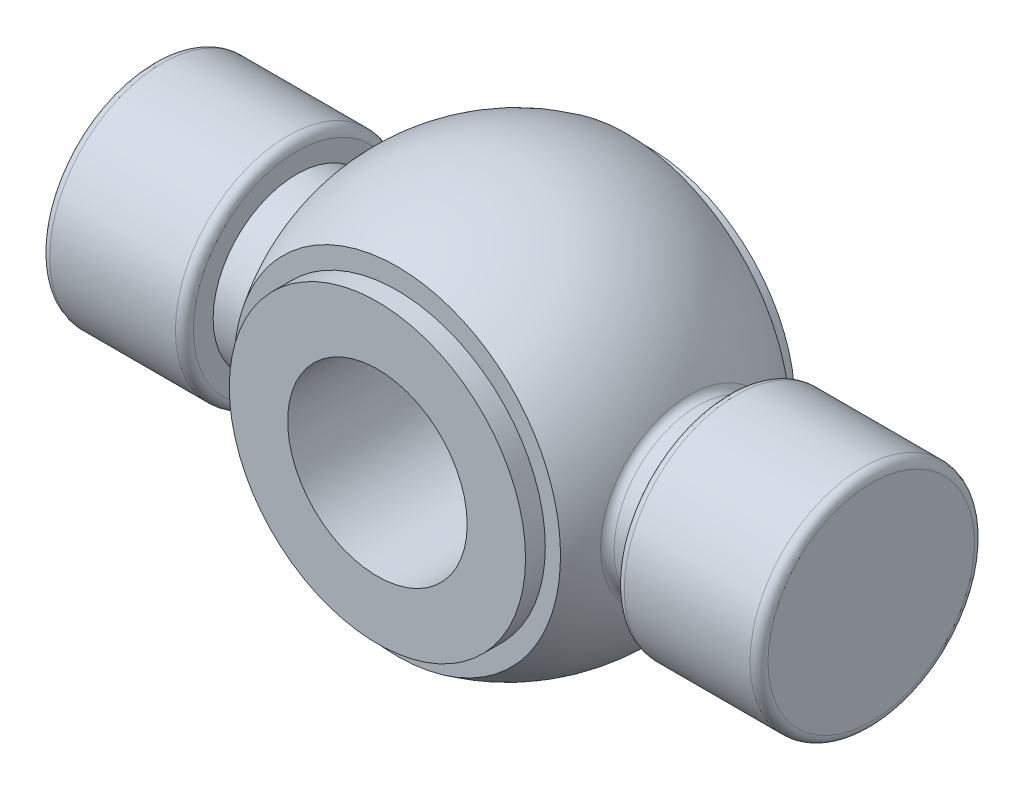
SolidWorks part; units mm, degrees
ref_plane "Front" through (0, 0, 0) normal (0, 0, 1) x (1, 0, 0)
ref_plane "Top" through (0, 0, 0) normal (0, 1, 0) x (1, 0, 0)
ref_plane "Right" through (0, 0, 0) normal (1, 0, 0) x (0, 0, -1)
sketch "Sketch1" plane through (0, 0, 0) normal (0, 0, 1) x (1, 0, 0)
  line L0 (-25.4, 0) -> (-25.4, 7.9375)
  line L1 (-25.4, 7.9375) -> (-15.24, 7.9375)
  line L2 (-12.7, 5.9055) -> (12.7, 5.9055) construction
  line L3 (12.7, 5.9055) -> (15.24, 5.9055)
  line L4 (25.4, 7.9375) -> (25.4, 0)
  line L5 (25.4, 0) -> (-25.4, 0)
  line L6 (-40.557, 0) -> (103.3272, 0) construction
  line L7 (0, 0) -> (0, 48.3914) construction
  line L8 (-15.24, 7.9375) -> (-15.24, 5.9055)
  line L9 (-15.24, 5.9055) -> (-12.7, 5.9055)
  line L10 (15.24, 5.9055) -> (15.24, 7.9375)
  line L11 (15.24, 7.9375) -> (25.4, 7.9375)
  arc A0 (12.7, 5.9055) -> (-12.7, 5.9055) centre (0, 0.7249) ccw
  dimension "D4" = 13.716
  dimension "D1" = 10.16
  dimension "D2" = 50.8
  dimension "D3" = 15.875
  dimension "D5" = 11.811
  dimension "D6" = 25.4
revolve "Revolve1" add sketch "Sketch1" angle 360 about L6
sketch "Sketch2" plane through (0, 0, 0) normal (0, 1, 0) x (1, 0, 0)
  line L0 (-25.4, 0) -> (0, 0) construction
  line L1 (-12.7, 8.128) -> (12.7, 8.128)
  line L2 (-12.7, 8.128) -> (-12.7, -8.128) construction
  line L3 (-12.7, -8.128) -> (12.7, -8.128)
  line L4 (12.7, 8.128) -> (12.7, -8.128) construction
  line L5 (-12.7, 8.128) -> (12.7, -8.128) construction
  line L6 (-12.7, -8.128) -> (12.7, 8.128) construction
  line L7 (-25.4, 7.9375) -> (-25.4, -7.9375) construction
  line L8 (0, -0.7249) -> (0, 0) construction
  line L9 (-12.7, 8.128) -> (-12.7, 23.2968)
  line L10 (-12.7, 23.2968) -> (12.7, 23.2968)
  line L11 (12.7, 23.2968) -> (12.7, 8.128)
  line L12 (12.7, -8.128) -> (12.7, -23.6661)
  line L13 (12.7, -23.6661) -> (-12.7, -23.6661)
  line L14 (-12.7, -23.6661) -> (-12.7, -8.128)
  arc A0 (-12.7, -5.9055) -> (12.7, -5.9055) centre (0, -0.7249) ccw construction
  arc A1 (-12.7, -5.9055) -> (12.7, -5.9055) centre (0, -0.7249) ccw
  point P0 (0, 0)
  dimension "D1" = 16.256
  dimension "D2" = 25.4
extrude "Cut-Extrude1" cut sketch "Sketch2" against normal through all and the other way through all contours L9 L10 L11 L1 | L14 L3 L12 L13
sketch "Sketch3" plane through (0, 0, 0) normal (0, 0, 1) x (1, 0, 0)
  circle A0 centre (0, 0) radius 10.4775
  dimension "D1" = 20.955
extrude "Boss-Extrude1" add sketch "Sketch3" along normal mid plane 19.05
sketch "Sketch4" plane through (0, 0, 9.525) normal (0, 0, 1) x (1, 0, 0)
  circle A0 centre (0, 0) radius 6.35
  dimension "D1" = 12.7
extrude "Cut-Extrude2" cut sketch "Sketch4" against normal through all
fillet "Fillet1" radius 0.635 6 edges at (25.4, 0, 7.9375) (-25.4, 0, 7.9375) (-12.7, 0, 5.9055) (12.7, 0, 5.9055) (-15.24, 0, 7.9375) (15.24, 0, 7.9375)
